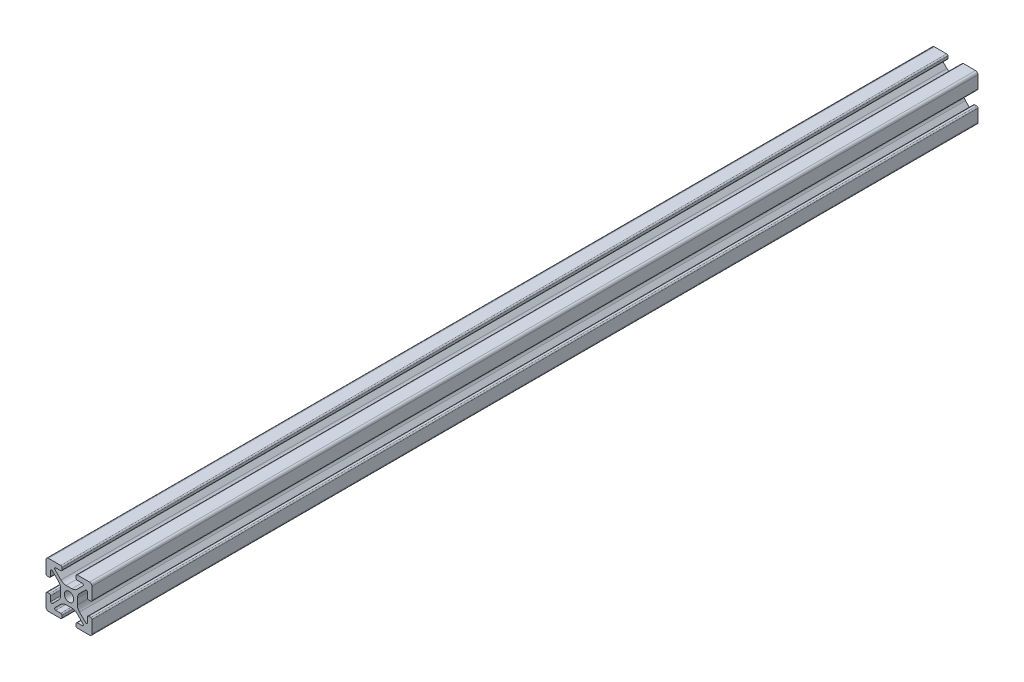
SolidWorks part; units mm, degrees
ref_plane "Front Plane" through (0, 0, 0) normal (0, 0, 1) x (1, 0, 0)
ref_plane "Top Plane" through (0, 0, 0) normal (0, 1, 0) x (1, 0, 0)
ref_plane "Right Plane" through (0, 0, 0) normal (1, 0, 0) x (0, 0, -1)
sketch "Sketch2" plane through (0, 0, 0) normal (0, 0, 1) x (1, 0, 0)
  line L0 (-3.6422, 1.2878) -> (-3.6422, -1.2878)
  line L1 (-1.2878, 3.6422) -> (1.2878, 3.6422)
  line L2 (-9.4433, 3.069) -> (-8.553, 3.069)
  line L3 (0, 0) -> (-15.7854, 0) construction
  line L4 (-3.4964, 4.5571) -> (-6.1213, 7.182)
  line L5 (-3.622, 8) -> (-5.7825, 8)
  line L6 (-3.069, 9.4433) -> (-3.069, 8.553)
  line L7 (-3.622, 10) -> (-8.939, 10)
  line L8 (0, 0) -> (0, 15.0393) construction
  line L9 (10, 3.622) -> (10, 8.939)
  line L10 (8, 3.622) -> (8, 5.7825)
  line L11 (4.5571, 3.4964) -> (7.182, 6.1213)
  line L12 (3.622, 10) -> (8.939, 10)
  line L13 (3.069, 9.4433) -> (3.069, 8.553)
  line L14 (3.622, 8) -> (5.7825, 8)
  line L15 (3.4964, 4.5571) -> (6.1213, 7.182)
  line L16 (9.4433, 3.069) -> (8.553, 3.069)
  line L17 (3.6422, 1.2878) -> (3.6422, -1.2878)
  line L18 (-10, -3.622) -> (-10, -8.939)
  line L19 (-8, -3.622) -> (-8, -5.7825)
  line L20 (-4.5571, -3.4964) -> (-7.182, -6.1213)
  line L21 (9.4433, -3.069) -> (8.553, -3.069)
  line L22 (3.4964, -4.5571) -> (6.1213, -7.182)
  line L23 (3.622, -8) -> (5.7825, -8)
  line L24 (3.069, -9.4433) -> (3.069, -8.553)
  line L25 (3.622, -10) -> (8.939, -10)
  line L26 (4.5571, -3.4964) -> (7.182, -6.1213)
  line L27 (8, -3.622) -> (8, -5.7825)
  line L28 (10, -3.622) -> (10, -8.939)
  line L29 (-3.622, -10) -> (-8.939, -10)
  line L30 (-3.069, -9.4433) -> (-3.069, -8.553)
  line L31 (-3.622, -8) -> (-5.7825, -8)
  line L32 (-3.4964, -4.5571) -> (-6.1213, -7.182)
  line L33 (-9.4433, -3.069) -> (-8.553, -3.069)
  line L34 (-1.2878, -3.6422) -> (1.2878, -3.6422)
  line L48 (-4.5571, 3.4964) -> (-7.182, 6.1213)
  line L49 (-8, 3.622) -> (-8, 5.7825)
  line L52 (-10, 3.622) -> (-10, 8.939)
  arc A0 (-8.553, 3.069) -> (-8, 3.622) centre (-8.553, 3.622) ccw
  arc A1 (-8, 5.7825) -> (-7.182, 6.1213) centre (-7.5208, 5.7825) cw
  arc A2 (-4.5571, 3.4964) -> (-3.6422, 1.2878) centre (-6.7657, 1.2878) cw
  arc A3 (-3.4964, 4.5571) -> (-1.2878, 3.6422) centre (-1.2878, 6.7657) ccw
  arc A4 (-5.7825, 8) -> (-6.1213, 7.182) centre (-5.7825, 7.5208) ccw
  arc A5 (-3.622, 10) -> (-3.069, 9.4433) centre (-3.622, 9.447) cw
  arc A6 (-3.069, 8.553) -> (-3.622, 8) centre (-3.622, 8.553) cw
  arc A7 (8.939, 10) -> (10, 8.939) centre (8.939, 8.939) cw
  arc A8 (10, 3.622) -> (9.4433, 3.069) centre (9.447, 3.622) cw
  arc A9 (3.069, 8.553) -> (3.622, 8) centre (3.622, 8.553) ccw
  arc A10 (3.622, 10) -> (3.069, 9.4433) centre (3.622, 9.447) ccw
  arc A11 (5.7825, 8) -> (6.1213, 7.182) centre (5.7825, 7.5208) cw
  arc A12 (3.4964, 4.5571) -> (1.2878, 3.6422) centre (1.2878, 6.7657) cw
  arc A13 (4.5571, 3.4964) -> (3.6422, 1.2878) centre (6.7657, 1.2878) ccw
  arc A14 (8, 5.7825) -> (7.182, 6.1213) centre (7.5208, 5.7825) ccw
  arc A15 (8.553, 3.069) -> (8, 3.622) centre (8.553, 3.622) cw
  arc A16 (-8.939, -10) -> (-10, -8.939) centre (-8.939, -8.939) cw
  arc A17 (-10, -3.622) -> (-9.4433, -3.069) centre (-9.447, -3.622) cw
  arc A18 (8.553, -3.069) -> (8, -3.622) centre (8.553, -3.622) ccw
  arc A19 (8, -5.7825) -> (7.182, -6.1213) centre (7.5208, -5.7825) cw
  arc A20 (4.5571, -3.4964) -> (3.6422, -1.2878) centre (6.7657, -1.2878) cw
  arc A21 (3.4964, -4.5571) -> (1.2878, -3.6422) centre (1.2878, -6.7657) ccw
  arc A22 (5.7825, -8) -> (6.1213, -7.182) centre (5.7825, -7.5208) ccw
  arc A23 (3.622, -10) -> (3.069, -9.4433) centre (3.622, -9.447) cw
  arc A24 (3.069, -8.553) -> (3.622, -8) centre (3.622, -8.553) cw
  arc A25 (10, -3.622) -> (9.4433, -3.069) centre (9.447, -3.622) ccw
  arc A26 (8.939, -10) -> (10, -8.939) centre (8.939, -8.939) ccw
  arc A27 (-3.069, -8.553) -> (-3.622, -8) centre (-3.622, -8.553) ccw
  arc A28 (-3.622, -10) -> (-3.069, -9.4433) centre (-3.622, -9.447) ccw
  arc A29 (-5.7825, -8) -> (-6.1213, -7.182) centre (-5.7825, -7.5208) cw
  arc A30 (-3.4964, -4.5571) -> (-1.2878, -3.6422) centre (-1.2878, -6.7657) cw
  arc A31 (-4.5571, -3.4964) -> (-3.6422, -1.2878) centre (-6.7657, -1.2878) ccw
  arc A32 (-8, -5.7825) -> (-7.182, -6.1213) centre (-7.5208, -5.7825) ccw
  arc A33 (-8.553, -3.069) -> (-8, -3.622) centre (-8.553, -3.622) cw
  arc A51 (-10, 3.622) -> (-9.4433, 3.069) centre (-9.447, 3.622) ccw
  arc A56 (-8.939, 10) -> (-10, 8.939) centre (-8.939, 8.939) ccw
  circle A57 centre (0, 0) radius 2.05
  point P1 (-3.6422, 0)
  point P46 (0, 0)
  point P48 (0, 0)
  point P53 (0, 3.6422)
  point P60 (0, 0)
  point P61 (0, 0)
  point P62 (0, 0)
  point P74 (0, 0)
  point P85 (0, 0)
  point P87 (0, 0)
  point P99 (0, 0)
  point P101 (0, 0)
  point P102 (0, 0)
  point P116 (0, -3.6422)
  point P117 (3.6422, 0)
  point P123 (0, 0)
  point P125 (0, 0)
  point P127 (0, 0)
  point P139 (0, 0)
  point P140 (0, 0)
  point P141 (0, 0)
  point P142 (0, 0)
  point P179 (0, 0)
  point P192 (0, 0)
  point P193 (0, 0)
  dimension "D1" = 0.553
  dimension "D3" = 3.1235
  dimension "D4" = 0.553
  dimension "D2" = 0.4792
  dimension "D5" = 1.061
  dimension "D6" = 2.05
extrude "Boss-Extrude2" add sketch "Sketch2" against normal blind 385
